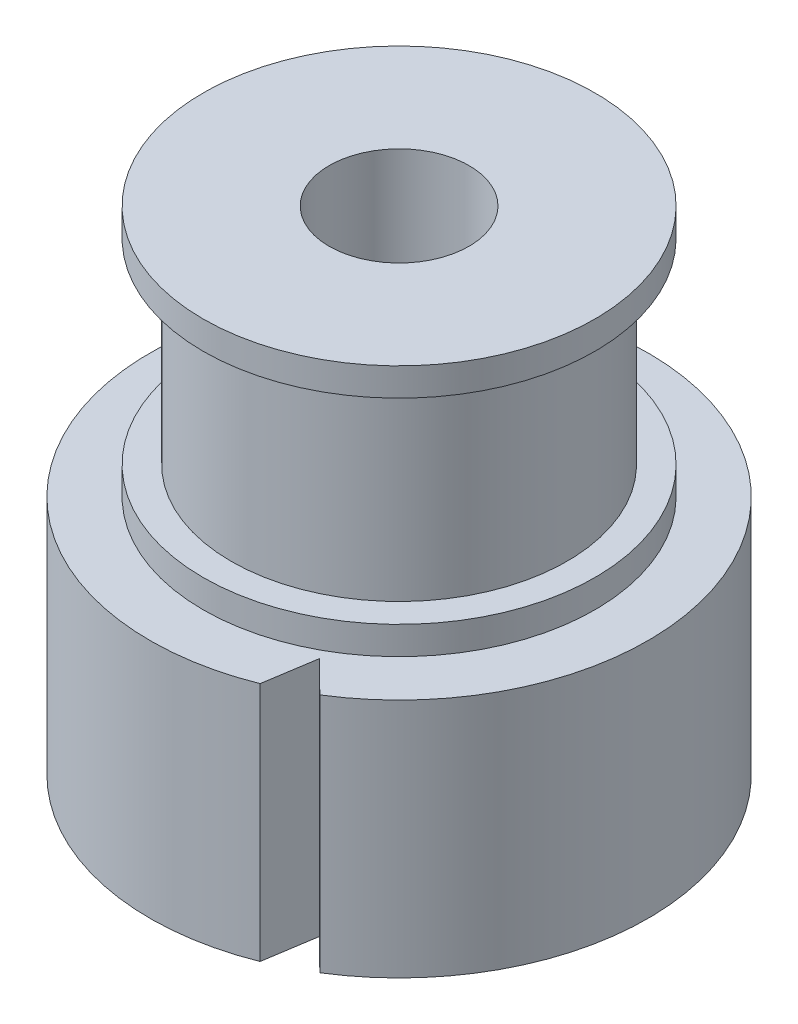
SolidWorks part; units mm, degrees
ref_plane "Alzado" through (0, 0, 0) normal (0, 0, 1) x (1, 0, 0)
ref_plane "Planta" through (0, 0, 0) normal (0, 1, 0) x (1, 0, 0)
ref_plane "Vista lateral" through (0, 0, 0) normal (1, 0, 0) x (0, 0, -1)
sketch "Croquis1" plane through (0, 0, 0) normal (0, 1, 0) x (1, 0, 0)
  circle A0 centre (0, 0) radius 2.5
  circle A1 centre (0, 0) radius 8.9
  dimension "D1" = 5
  dimension "D2" = 17.8
extrude "Saliente-Extruir1" add sketch "Croquis1" along normal blind 8.6
sketch "Croquis2" plane through (0, 8.6, 0) normal (0, 1, 0) x (1, 0, 0)
  circle A0 centre (0, 0) radius 7
  circle A1 centre (0, 0) radius 2.5
  dimension "D1" = 14
  dimension "D2" = 5
extrude "Saliente-Extruir2" add sketch "Croquis2" along normal blind 1
sketch "Croquis3" plane through (0, 9.6, 0) normal (0, 1, 0) x (1, 0, 0)
  circle A0 centre (0, 0) radius 2.5
  circle A1 centre (0, 0) radius 6
  dimension "D1" = 5
  dimension "D2" = 12
extrude "Saliente-Extruir3" add sketch "Croquis3" along normal blind 7
sketch "Croquis4" plane through (0, 16.6, 0) normal (0, 1, 0) x (1, 0, 0)
  circle A0 centre (0, 0) radius 2.5
  circle A1 centre (0, 0) radius 7
  dimension "D1" = 5
  dimension "D2" = 14
extrude "Saliente-Extruir4" add sketch "Croquis4" along normal blind 1
sketch "Croquis7" plane through (0, 8.6, 0) normal (0, 1, 0) x (1, 0, 0)
  line L0 (3.2996, -8.2657) -> (3.5854, -6.4334)
  line L1 (3.5854, -6.4334) -> (4.7155, -7.5481)
  circle A1 centre (0, 0) radius 8.9
  arc A2 (3.2996, -8.2657) -> (4.7155, -7.5481) centre (0, 0) ccw
  dimension "D2" = 1.8324
  dimension "D3" = 1.5874
  dimension "D1" = 0
extrude "Cortar-Extruir1" cut sketch "Croquis7" against normal through all
